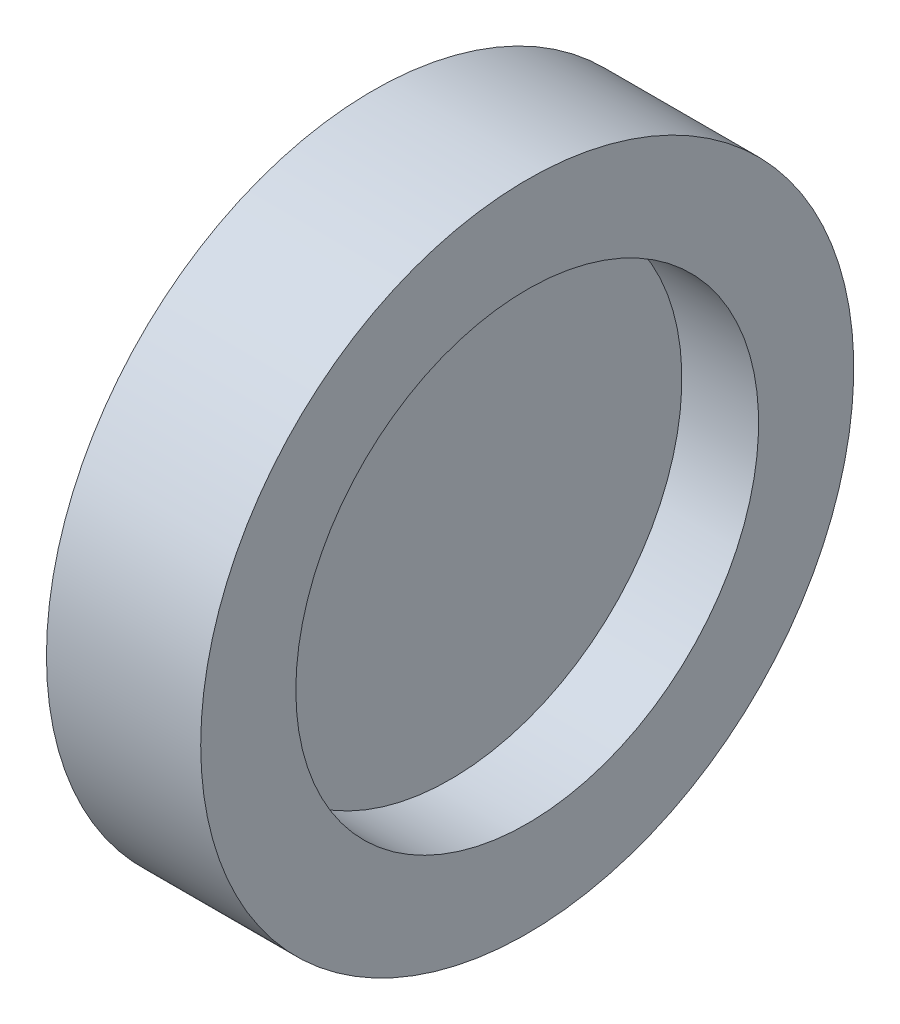
SolidWorks part; units mm, degrees
ref_plane "前视基准面" through (0, 0, 0) normal (0, 0, 1) x (1, 0, 0)
ref_plane "上视基准面" through (0, 0, 0) normal (0, 1, 0) x (1, 0, 0)
ref_plane "右视基准面" through (0, 0, 0) normal (1, 0, 0) x (0, 0, -1)
sketch "草图1" plane through (0, 0, 0) normal (0, 0, 1) x (1, 0, 0)
  line L0 (-0.0135, 9) -> (-0.0135, 0)
  line L2 (-0.0135, 9) -> (0.0135, 9)
  line L3 (-0.0135, 0) -> (0.0135, 0)
  line L4 (0.0135, 9) -> (0.0135, 0)
revolve "旋转2" add sketch "草图1" angle 360 about L3
sketch "草图4" plane through (0, 0, 0) normal (0, 0, 1) x (1, 0, 0)
  line L0 (-3, 12.7) -> (3, 12.7)
  line L1 (3, 12.7) -> (3, 9)
  line L2 (3, 9) -> (-3, 9)
  line L3 (0.0135, 9) -> (-0.0135, 9) construction
  line L4 (-3, 9) -> (-3, 12.7)
  line L5 (0, 9) -> (0, 12.7) construction
  line L6 (-1.6142, 0) -> (1.5903, 0) construction
revolve "旋转3" add sketch "草图4" angle 360 about L6
equation "\"D1@草图4\"=\"D1@草图1\""
